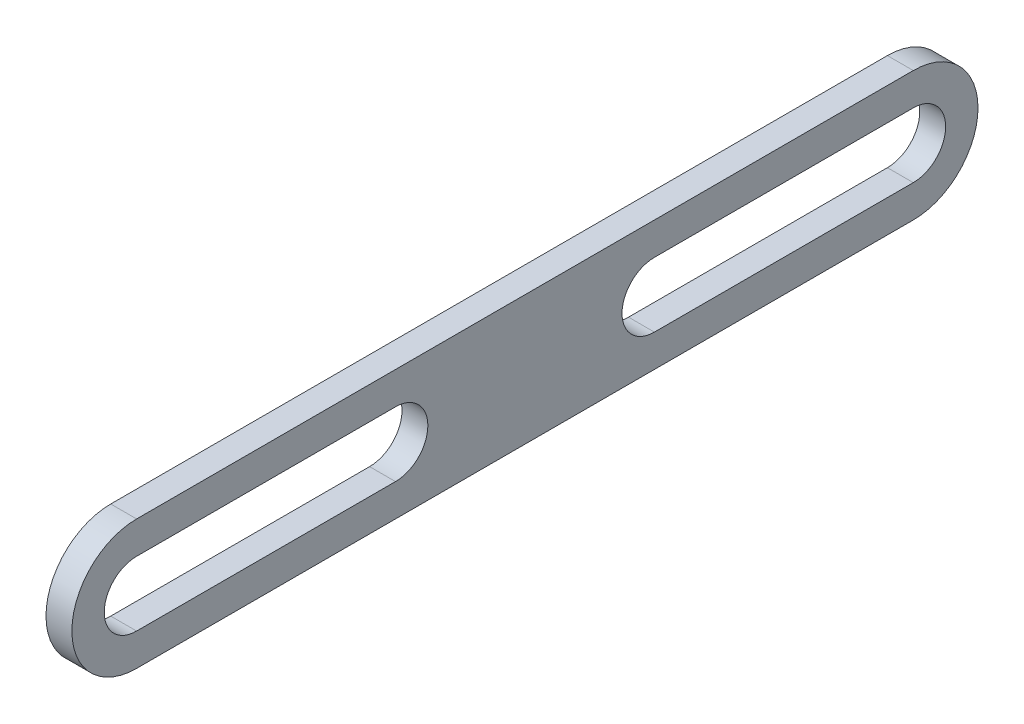
SolidWorks part; units mm, degrees
ref_plane "Front Plane" through (0, 0, 0) normal (0, 0, 1) x (1, 0, 0)
ref_plane "Top Plane" through (0, 0, 0) normal (0, 1, 0) x (1, 0, 0)
ref_plane "Right Plane" through (0, 0, 0) normal (1, 0, 0) x (0, 0, -1)
sketch "Sketch1" plane through (0, 0, 0) normal (1, 0, 0) x (0, 0, -1)
  line L0 (-38.1, 0) -> (38.1, 0) construction
  line L1 (-38.1, 6.35) -> (38.1, 6.35)
  line L2 (-38.1, -6.35) -> (38.1, -6.35)
  arc A0 (-38.1, 6.35) -> (-38.1, -6.35) centre (-38.1, 0) ccw
  arc A1 (38.1, -6.35) -> (38.1, 6.35) centre (38.1, 0) ccw
  point P3 (0, 0)
  dimension "D2" = 6.35
  dimension "D1" = 76.2
extrude "Boss-Extrude1" add sketch "Sketch1" along normal mid plane 2.54
sketch "Sketch2" plane through (1.27, 0, 0) normal (1, 0, 0) x (0, 0, -1)
  line L0 (-38.1, 0) -> (-12.7, 0) construction
  line L1 (-38.1, 3.175) -> (-12.7, 3.175)
  line L2 (-38.1, -3.175) -> (-12.7, -3.175)
  line L3 (0, 1.397) -> (0, -1.397) construction
  line L6 (38.1, 0) -> (12.7, 0) construction
  line L7 (38.1, 3.175) -> (12.7, 3.175)
  line L8 (38.1, -3.175) -> (12.7, -3.175)
  arc A0 (-38.1, 3.175) -> (-38.1, -3.175) centre (-38.1, 0) ccw
  arc A1 (-12.7, -3.175) -> (-12.7, 3.175) centre (-12.7, 0) ccw
  arc A4 (-38.1, 6.35) -> (-38.1, -6.35) centre (-38.1, 0) ccw construction
  arc A5 (38.1, 3.175) -> (38.1, -3.175) centre (38.1, 0) cw
  arc A6 (12.7, -3.175) -> (12.7, 3.175) centre (12.7, 0) cw
  point P3 (-25.4, 0)
  point P15 (25.4, 0)
  dimension "D2" = 3.175
  dimension "D1" = 25.4
extrude "Cut-Extrude1" cut sketch "Sketch2" against normal through all
